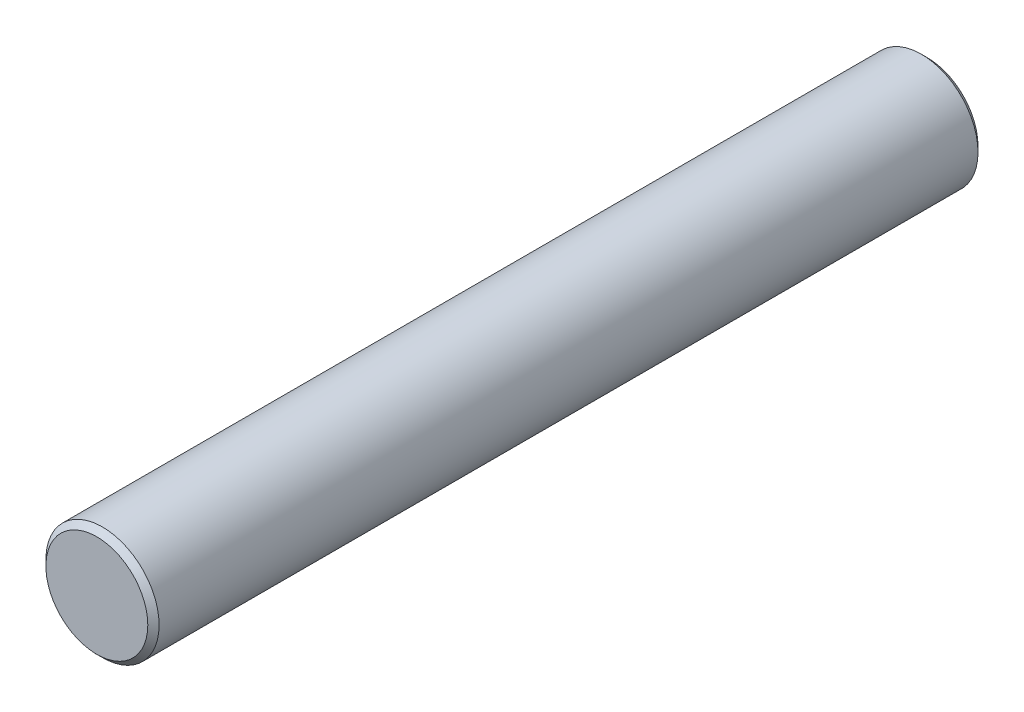
SolidWorks part; units mm, degrees
material "Plain Carbon Steel"
ref_plane "Front Plane" through (0, 0, 0) normal (0, 0, 1) x (1, 0, 0)
ref_plane "Top Plane" through (0, 0, 0) normal (0, 1, 0) x (1, 0, 0)
ref_plane "Right Plane" through (0, 0, 0) normal (1, 0, 0) x (0, 0, -1)
sketch "Sketch1" plane through (0, 0, 0) normal (0, 0, 1) x (1, 0, 0)
  circle A0 centre (0, 0) radius 1.5
  dimension "D1" = 3
extrude "Boss-Extrude1" add sketch "Sketch1" along normal mid plane 22
chamfer "Chamfer1" distance 0.15 angle 45 2 edges at (1.5, 0, -11) (1.5, 0, 11)
